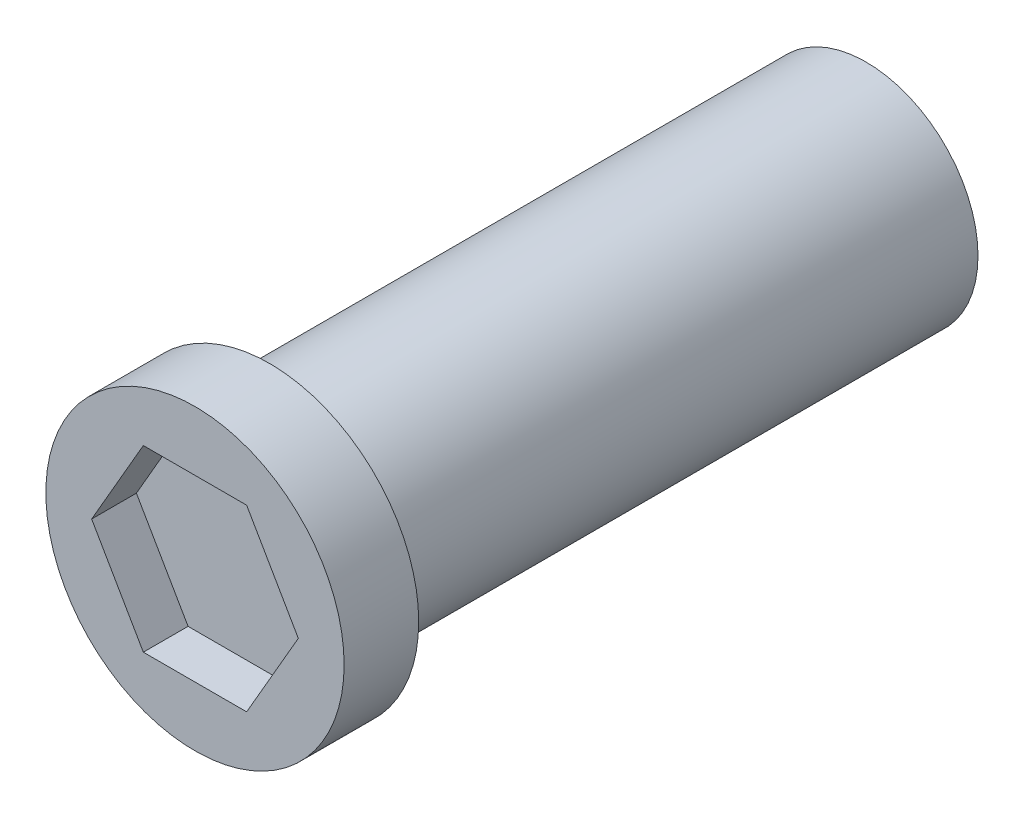
SolidWorks part; units mm, degrees
ref_plane "Front Plane" through (0, 0, 0) normal (0, 0, 1) x (1, 0, 0)
ref_plane "Top Plane" through (0, 0, 0) normal (0, 1, 0) x (1, 0, 0)
ref_plane "Right Plane" through (0, 0, 0) normal (1, 0, 0) x (0, 0, -1)
sketch "Sketch1" plane through (0, 0, 0) normal (0, 0, 1) x (1, 0, 0)
  circle A0 centre (0, 0) radius 7.5
  dimension "D1" = 15
extrude "Boss-Extrude1" add sketch "Sketch1" along normal blind 40
sketch "Sketch2" plane through (0, 0, 40) normal (0, 0, 1) x (1, 0, 0)
  circle A0 centre (0, 0) radius 10
  dimension "D1" = 20
extrude "Boss-Extrude2" add sketch "Sketch2" along normal blind 5
sketch "Sketch3" plane through (0, 0, 45) normal (0, 0, 1) x (1, 0, 0)
  line L1 (-6.9282, 0) -> (-3.4641, -6)
  line L2 (-3.4641, -6) -> (3.4641, -6)
  line L3 (3.4641, -6) -> (6.9282, 0)
  line L4 (6.9282, 0) -> (3.4641, 6)
  line L5 (3.4641, 6) -> (-3.4641, 6)
  line L6 (-3.4641, 6) -> (-6.9282, 0)
  circle A0 centre (0, 0) radius 6 construction
  point P1 (0, 6)
  dimension "D1" = 12
extrude "Cut-Extrude1" cut sketch "Sketch3" against normal blind 3
